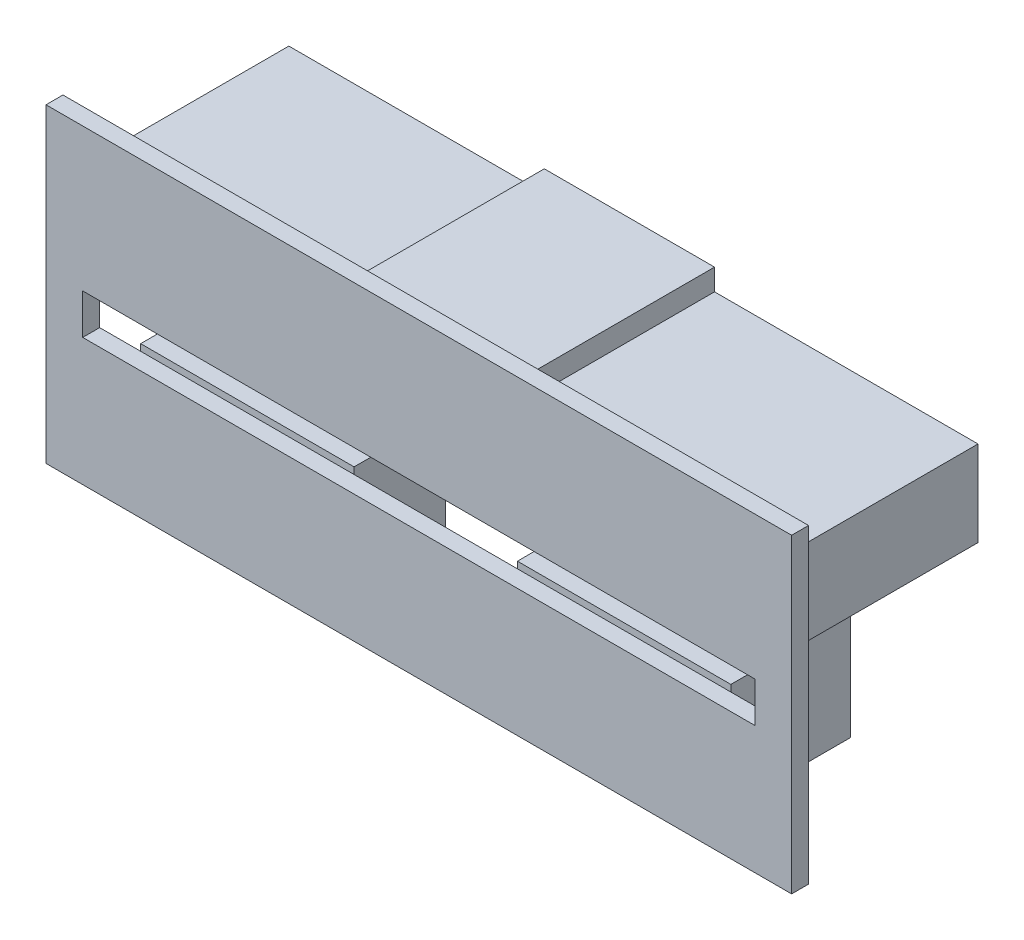
SolidWorks part; units mm, degrees
ref_plane "Alzado" through (0, 0, 0) normal (0, 0, 1) x (1, 0, 0)
ref_plane "Planta" through (0, 0, 0) normal (0, 1, 0) x (1, 0, 0)
ref_plane "Vista lateral" through (0, 0, 0) normal (1, 0, 0) x (0, 0, -1)
sketch "Croquis1" plane through (0, 0, 0) normal (0, 0, 1) x (1, 0, 0)
  line L1 (26.404, 7.6) -> (-26.404, 7.6)
  line L2 (26.404, 7.6) -> (26.404, -14.4)
  line L3 (26.404, -14.4) -> (-26.404, -14.4)
  line L4 (-26.404, 7.6) -> (-26.404, -14.4)
sketch "Croquis2" plane through (0, -12.4, 0) normal (0, 1, 0) x (1, 0, 0)
  line L0 (20.9, 8.4686) -> (20.9, 0)
  line L1 (20.9, 0) -> (20.9, 10.2) construction
  line L2 (26.404, 0) -> (-26.404, 0) construction
  line L3 (20.9, 0) -> (5.7883, 0)
  line L4 (5.7883, 0) -> (5.745, 6.4201)
  line L5 (5.745, 0) -> (5.745, 23.6848) construction
  line L6 (12.95, 10.2) -> (-12.95, 10.2) construction
  line L7 (0, 6.0165) -> (0, 0) construction
  line L8 (-5.7883, 0) -> (-5.745, 6.4201)
  line L9 (-20.9, 8.4686) -> (-20.9, 0)
  line L10 (-20.9, 0) -> (-5.7883, 0)
  arc A0 (5.745, 6.4201) -> (20.9, 8.4686) centre (12.95, 10.2) ccw
  arc A1 (-20.9, 8.4686) -> (-5.745, 6.4201) centre (-12.95, 10.2) ccw
  arc A2 (-5.745, 6.4201) -> (-20.9, 8.4686) centre (-12.95, 10.2) cw
  line M5 (20.9, 0) -> (20.9, 10.2)
  line M8 (5, 0) -> (20.9, 0)
extrude "Saliente-Extruir1" add sketch "Croquis2" along normal up to surface (7.5 mm away) contours A0 L4 M8 M5 | A1 L9 L10 L8
sketch "Croquis3" plane through (0, 0, 0) normal (0, 0, 1) x (1, 0, 0)
  line L0 (24.404, 4.6) -> (24.404, 1.9024)
  line L1 (24.404, 4.6) -> (24.404, -14.4) construction
  line L2 (22.804, 1.9024) -> (-22.804, 1.9024)
  line L3 (-24.404, 4.6) -> (-24.404, -14.4) construction
  line L4 (-24.404, 1.9024) -> (-24.404, 4.6)
  line L5 (-24.404, 4.6) -> (-6.3129, 4.6)
  line L6 (-6.3129, 4.6) -> (-6.3129, 6.1175)
  line L7 (-6.3129, 6.1175) -> (5.745, 6.1175)
  line L8 (5.745, 6.1175) -> (5.745, 4.6)
  line L9 (5.745, 4.6) -> (24.404, 4.6)
  line L10 (0, 7.6) -> (0, 1.9024) construction
  line L11 (26.404, 7.6) -> (-26.404, 7.6) construction
  line L12 (-24.404, -1.4525) -> (-24.404, 1.9024)
  line L13 (-24.404, 4.6) -> (-24.404, -3.6) construction
  line L14 (-24.404, -1.4525) -> (-22.804, -1.4525)
  line L15 (-22.804, -1.4525) -> (-22.804, 1.9024)
  line L16 (-24.404, -1.4525) -> (-24.404, 1.9024)
  line L17 (24.404, -1.4525) -> (24.404, 1.9024)
  line L18 (24.404, -1.4525) -> (22.804, -1.4525)
  line L19 (22.804, -1.4525) -> (22.804, 1.9024)
  line M9 (5.745, 6.1175) -> (5.745, 4.6)
  line M10 (5.745, 4.6) -> (24.404, 4.6)
  line M11 (24.404, 4.6) -> (24.404, -14.4)
  line M17 (-24.404, -14.4) -> (-24.404, 4.6)
  line M18 (-24.404, 4.6) -> (-6.3129, 4.6)
  line M19 (-6.3129, 4.6) -> (-6.3129, 6.1175)
  line M20 (-6.3129, 6.1175) -> (5.745, 6.1175)
extrude "Saliente-Extruir2" add sketch "Croquis3" against normal blind 14 separate body contours L7 L10 L2 L19 L18 M11 M10 M9 | L10 L14 L15 L2 M20 M19 M18 M17
sketch "Croquis4" plane through (0, 0, 0) normal (0, 0, 1) x (1, 0, 0)
  line L1 (26.404, 7.6) -> (-26.404, 7.6)
  line L2 (26.404, 7.6) -> (26.404, -14.4)
  line L3 (26.404, -14.4) -> (-26.404, -14.4)
  line L4 (-26.404, 7.6) -> (-26.404, -14.4)
  line L5 (23.8218, -2.5175) -> (-23.8033, -2.5175)
  line L6 (23.8218, -2.5175) -> (23.8218, -5.369)
  line L7 (23.8218, -5.369) -> (-23.8033, -5.369)
  line L8 (-23.8033, -2.5175) -> (-23.8033, -5.369)
extrude "Saliente-Extruir3" add sketch "Croquis4" along normal blind 1.2
